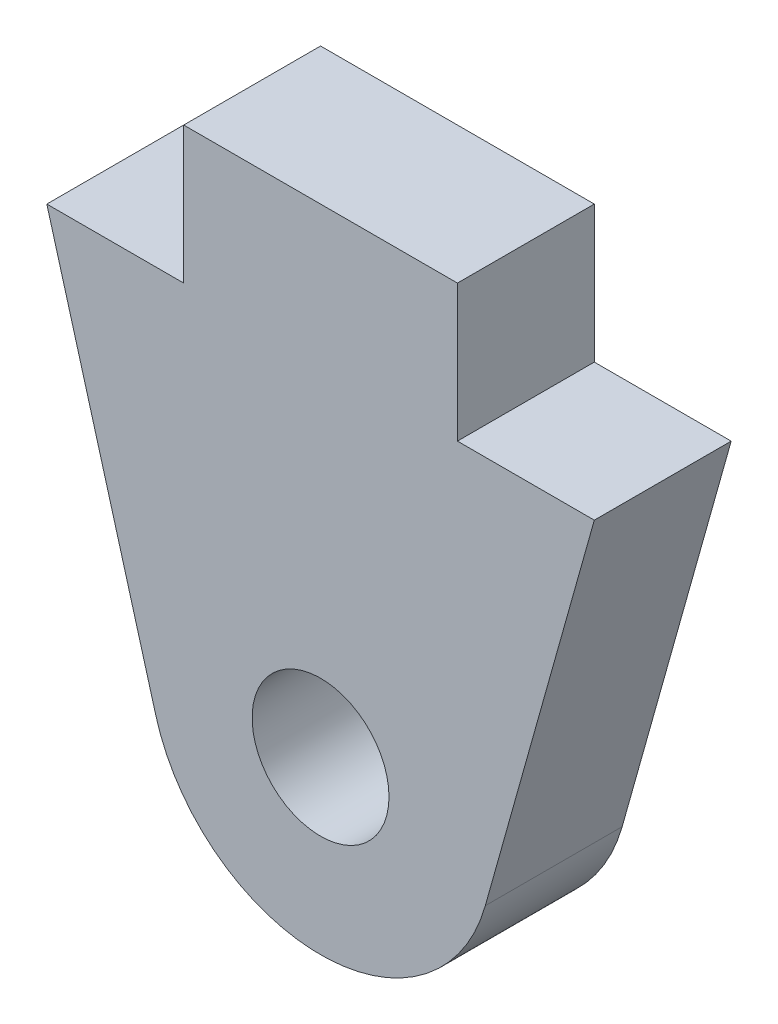
SolidWorks part; units mm, degrees
ref_plane "Front" through (0, 0, 0) normal (0, 0, 1) x (1, 0, 0)
ref_plane "Top" through (0, 0, 0) normal (0, 1, 0) x (1, 0, 0)
ref_plane "Right" through (0, 0, 0) normal (1, 0, 0) x (0, 0, -1)
sketch "Sketch1" plane through (0, 0, 0) normal (0, 0, 1) x (1, 0, 0)
  line L0 (-524.2133, 3.175) -> (-536.9133, 3.175)
  line L1 (-536.9133, 3.175) -> (-536.9133, -3.175)
  line L2 (-536.9133, -3.175) -> (-543.2633, -3.175)
  line L3 (-543.2633, -3.175) -> (-538.2054, -21.195)
  line L4 (-524.2133, 3.175) -> (-524.2133, -3.175)
  line L5 (-524.2133, -3.175) -> (-517.8633, -3.175)
  line L6 (-517.8633, -3.175) -> (-522.9211, -21.195)
  arc A0 (-522.9211, -21.195) -> (-538.2054, -21.195) centre (-530.5633, -19.05) cw
  circle A1 centre (-530.5633, -19.05) radius 3.175
  point P15 (-530.5633, 3.175)
  dimension "D2" = 6.35
  dimension "D3" = 7.9375
  dimension "D1" = 6.35
extrude "Boss-Extrude1" add sketch "Sketch1" along normal blind 6.35
